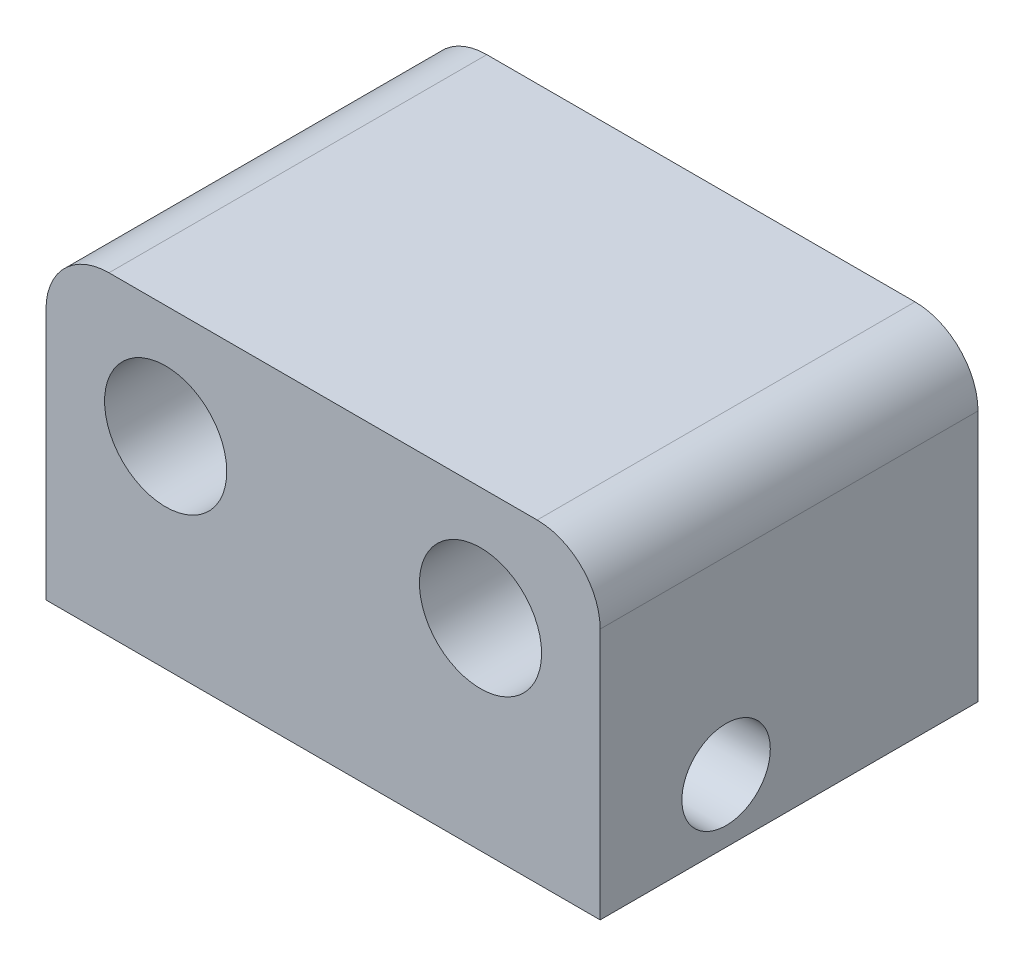
SolidWorks part; units mm, degrees
ref_plane "Front Plane" through (0, 0, 0) normal (0, 0, 1) x (1, 0, 0)
ref_plane "Top Plane" through (0, 0, 0) normal (0, 1, 0) x (1, 0, 0)
ref_plane "Right Plane" through (0, 0, 0) normal (1, 0, 0) x (0, 0, -1)
sketch "Sketch2" plane through (0, 0, 0) normal (0, 0, 1) x (1, 0, 0)
  line L0 (-11, 0) -> (11, 0) construction
  line L1 (-11, 25) -> (11, 25)
  line L2 (-11, 25) -> (-11, -25)
  line L3 (-11, -25) -> (11, -25)
  line L4 (11, 25) -> (11, -25)
  line L5 (-11, 12.5) -> (11, 12.5)
  line L6 (-11, 12.5) -> (-11, -12.5)
  line L7 (-11, -12.5) -> (11, -12.5)
  line L8 (11, 12.5) -> (11, -12.5)
  line L9 (-6.25, 20.5) -> (6.25, 20.5) construction
  circle A1 centre (0, -19.9) radius 2.425
  circle A2 centre (-6.25, 20.5) radius 2.425
  circle A3 centre (6.25, 20.5) radius 2.425
  point P4 (0, 25)
  point P6 (-11, 0)
  point P11 (0, 12.5)
  point P12 (11, 0)
  point P21 (0, 20.5)
  dimension "D5" = 4.85
  dimension "D1" = 22
  dimension "D2" = 50
  dimension "D3" = 22
  dimension "D4" = 25
  dimension "D6" = 12.5
  dimension "D7" = 8
extrude "Boss-Extrude1" add sketch "Sketch2" along normal blind 15 contours L2 L5 L4 L1 A3 A2
sketch "Sketch3" plane through (11, 0, 0) normal (1, 0, 0) x (0, 0, -1)
  line L1 (-10, 15) -> (-10, -15) construction
  circle A1 centre (-10, 15) radius 1.755
  dimension "D2" = 3.51
  dimension "D3" = 30
extrude "Cut-Extrude1" cut sketch "Sketch3" against normal blind 30
fillet "Fillet1" radius 2.5 2 edges at (-11, 25, 7.5) (11, 25, 7.5)
